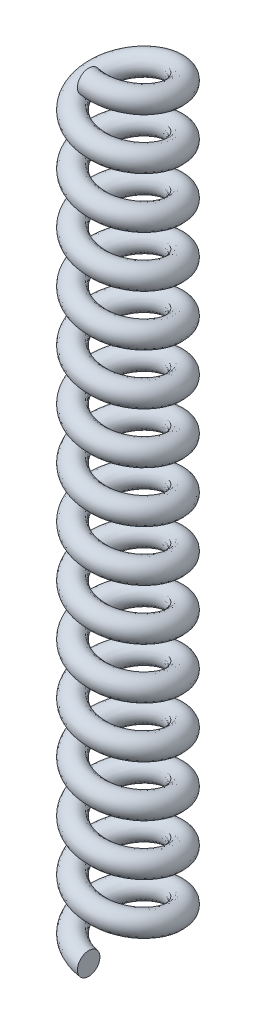
SolidWorks part; units mm, degrees
ref_plane "Alzado" through (0, 0, 0) normal (0, 0, 1) x (1, 0, 0)
ref_plane "Planta" through (0, 0, 0) normal (0, 1, 0) x (1, 0, 0)
ref_plane "Vista lateral" through (0, 0, 0) normal (1, 0, 0) x (0, 0, -1)
sketch "Croquis1" plane through (0, 0, 0) normal (0, 1, 0) x (1, 0, 0)
  circle A0 centre (0, 0) radius 3.5
  dimension "D1" = 7
curve "Hélice/Espiral1" pitch 4.5333 height 68 turns 15
sketch "Croquis2" plane through (0, 0, 0) normal (1, 0, 0) x (0, 0, -1)
  circle A0 centre (-3.5, 0) radius 1
  spline S0 degree 3 poles (-3.5, 0) (-3.5, 0.0939) (-3.3178, 0.2836) (-2.5393, 0.5666) (-1.3743, 0.85) (0, 1.1333) (1.3743, 1.4167) (2.5393, 1.7) (3.3178, 1.9833) (3.5911, 2.2667) (3.3178, 2.55) (2.5393, 2.8333) (0.9859, 3.2111) (-0.9859, 3.5889) (-2.5393, 3.9667) (-3.3178, 4.25) (-3.5911, 4.5333) (-3.3178, 4.8167) (-2.5393, 5.1) (-0.9859, 5.4778) (0.9859, 5.8556) (2.5393, 6.2333) (3.3178, 6.5167) (3.5911, 6.8) (3.3178, 7.0833) (2.5393, 7.3667) (0.9859, 7.7444) (-0.9859, 8.1222) (-2.5393, 8.5) (-3.3178, 8.7833) (-3.5911, 9.0667) (-3.3178, 9.35) (-2.5393, 9.6333) (-0.9859, 10.0111) (0.9859, 10.3889) (2.5393, 10.7667) (3.3178, 11.05) (3.5911, 11.3333) (3.3178, 11.6167) (2.5393, 11.9) (0.9859, 12.2778) (-0.9859, 12.6556) (-2.5393, 13.0333) (-3.3178, 13.3167) (-3.5911, 13.6) (-3.3178, 13.8833) (-2.5393, 14.1667) (-0.9859, 14.5444) (0.9859, 14.9222) (2.5393, 15.3) (3.3178, 15.5833) (3.5911, 15.8667) (3.3178, 16.15) (2.5393, 16.4333) (0.9859, 16.8111) (-0.9859, 17.1889) (-2.5393, 17.5667) (-3.3178, 17.85) (-3.5911, 18.1333) (-3.3178, 18.4167) (-2.5393, 18.7) (-0.9859, 19.0778) (0.9859, 19.4556) (2.5393, 19.8333) (3.3178, 20.1167) (3.5911, 20.4) (3.3178, 20.6833) (2.5393, 20.9667) (0.9859, 21.3444) (-0.9859, 21.7222) (-2.5393, 22.1) (-3.3178, 22.3833) (-3.5911, 22.6667) (-3.3178, 22.95) (-2.5393, 23.2333) (-0.9859, 23.6111) (0.9859, 23.9889) (2.5393, 24.3667) (3.3178, 24.65) (3.5911, 24.9333) (3.3178, 25.2167) (2.5393, 25.5) (0.9859, 25.8778) (-0.9859, 26.2556) (-2.5393, 26.6333) (-3.3178, 26.9167) (-3.5911, 27.2) (-3.3178, 27.4833) (-2.5393, 27.7667) (-0.9859, 28.1444) (0.9859, 28.5222) (2.5393, 28.9) (3.3178, 29.1833) (3.5911, 29.4667) (3.3178, 29.75) (2.5393, 30.0333) (0.9859, 30.4111) (-0.9859, 30.7889) (-2.5393, 31.1667) (-3.3178, 31.45) (-3.5911, 31.7333) (-3.3178, 32.0167) (-2.5393, 32.3) (-0.9859, 32.6778) (0.9859, 33.0556) (2.5393, 33.4333) (3.3178, 33.7167) (3.5911, 34) (3.3178, 34.2833) (2.5393, 34.5667) (0.9859, 34.9444) (-0.9859, 35.3222) (-2.5393, 35.7) (-3.3178, 35.9833) (-3.5911, 36.2667) (-3.3178, 36.55) (-2.5393, 36.8333) (-0.9859, 37.2111) (0.9859, 37.5889) (2.5393, 37.9667) (3.3178, 38.25) (3.5911, 38.5333) (3.3178, 38.8167) (2.5393, 39.1) (0.9859, 39.4778) (-0.9859, 39.8556) (-2.5393, 40.2333) (-3.3178, 40.5167) (-3.5911, 40.8) (-3.3178, 41.0833) (-2.5393, 41.3667) (-0.9859, 41.7444) (0.9859, 42.1222) (2.5393, 42.5) (3.3178, 42.7833) (3.5911, 43.0667) (3.3178, 43.35) (2.5393, 43.6333) (0.9859, 44.0111) (-0.9859, 44.3889) (-2.5393, 44.7667) (-3.3178, 45.05) (-3.5911, 45.3333) (-3.3178, 45.6167) (-2.5393, 45.9) (-0.9859, 46.2778) (0.9859, 46.6556) (2.5393, 47.0333) (3.3178, 47.3167) (3.5911, 47.6) (3.3178, 47.8833) (2.5393, 48.1667) (0.9859, 48.5444) (-0.9859, 48.9222) (-2.5393, 49.3) (-3.3178, 49.5833) (-3.5911, 49.8667) (-3.3178, 50.15) (-2.5393, 50.4333) (-0.9859, 50.8111) (0.9859, 51.1889) (2.5393, 51.5667) (3.3178, 51.85) (3.5911, 52.1333) (3.3178, 52.4167) (2.5393, 52.7) (0.9859, 53.0778) (-0.9859, 53.4556) (-2.5393, 53.8333) (-3.3178, 54.1167) (-3.5911, 54.4) (-3.3178, 54.6833) (-2.5393, 54.9667) (-0.9859, 55.3444) (0.9859, 55.7222) (2.5393, 56.1) (3.3178, 56.3833) (3.5911, 56.6667) (3.3178, 56.95) (2.5393, 57.2333) (0.9859, 57.6111) (-0.9859, 57.9889) (-2.5393, 58.3667) (-3.3178, 58.65) (-3.5911, 58.9333) (-3.3178, 59.2167) (-2.5393, 59.5) (-0.9859, 59.8778) (0.9859, 60.2556) (2.5393, 60.6333) (3.3178, 60.9167) (3.5911, 61.2) (3.3178, 61.4833) (2.5393, 61.7667) (0.9859, 62.1444) (-0.9859, 62.5222) (-2.5393, 62.9) (-3.3178, 63.1833) (-3.5911, 63.4667) (-3.3178, 63.75) (-2.5393, 64.0333) (-0.9859, 64.4111) (0.9859, 64.7889) (2.5393, 65.1667) (3.3178, 65.45) (3.5911, 65.7333) (3.3178, 66.0167) (2.5393, 66.3) (1.3743, 66.5833) (0, 66.8667) (-1.3743, 67.15) (-2.5393, 67.4334) (-3.3178, 67.7164) (-3.5, 67.9061) (-3.5, 68) knots 0 0 0 0 0.004167 0.008333 0.0125 0.016667 0.020833 0.025 0.029167 0.033333 0.0375 0.041667 0.045833 0.054167 0.058333 0.0625 0.066667 0.070833 0.075 0.079167 0.0875 0.091667 0.095833 0.1 0.104167 0.108333 0.1125 0.120833 0.125 0.129167 0.133333 0.1375 0.141667 0.145833 0.154167 0.158333 0.1625 0.166667 0.170833 0.175 0.179167 0.1875 0.191667 0.195833 0.2 0.204167 0.208333 0.2125 0.220833 0.225 0.229167 0.233333 0.2375 0.241667 0.245833 0.254167 0.258333 0.2625 0.266667 0.270833 0.275 0.279167 0.2875 0.291667 0.295833 0.3 0.304167 0.308333 0.3125 0.320833 0.325 0.329167 0.333333 0.3375 0.341667 0.345833 0.354167 0.358333 0.3625 0.366667 0.370833 0.375 0.379167 0.3875 0.391667 0.395833 0.4 0.404167 0.408333 0.4125 0.420833 0.425 0.429167 0.433333 0.4375 0.441667 0.445833 0.454167 0.458333 0.4625 0.466667 0.470833 0.475 0.479167 0.4875 0.491667 0.495833 0.5 0.504167 0.508333 0.5125 0.520833 0.525 0.529167 0.533333 0.5375 0.541667 0.545833 0.554167 0.558333 0.5625 0.566667 0.570833 0.575 0.579167 0.5875 0.591667 0.595833 0.6 0.604167 0.608333 0.6125 0.620833 0.625 0.629167 0.633333 0.6375 0.641667 0.645833 0.654167 0.658333 0.6625 0.666667 0.670833 0.675 0.679167 0.6875 0.691667 0.695833 0.7 0.704167 0.708333 0.7125 0.720833 0.725 0.729167 0.733333 0.7375 0.741667 0.745833 0.754167 0.758333 0.7625 0.766667 0.770833 0.775 0.779167 0.7875 0.791667 0.795833 0.8 0.804167 0.808333 0.8125 0.820833 0.825 0.829167 0.833333 0.8375 0.841667 0.845833 0.854167 0.858333 0.8625 0.866667 0.870833 0.875 0.879167 0.8875 0.891667 0.895833 0.9 0.904167 0.908333 0.9125 0.920833 0.925 0.929167 0.933333 0.9375 0.941667 0.945833 0.954167 0.958333 0.9625 0.966667 0.970833 0.975 0.979167 0.983333 0.9875 0.991667 0.995833 1 1 1 1 construction
  dimension "D1" = 2
sweep "Barrer1" add profiles "Croquis2" path "Hélice/Espiral1"
